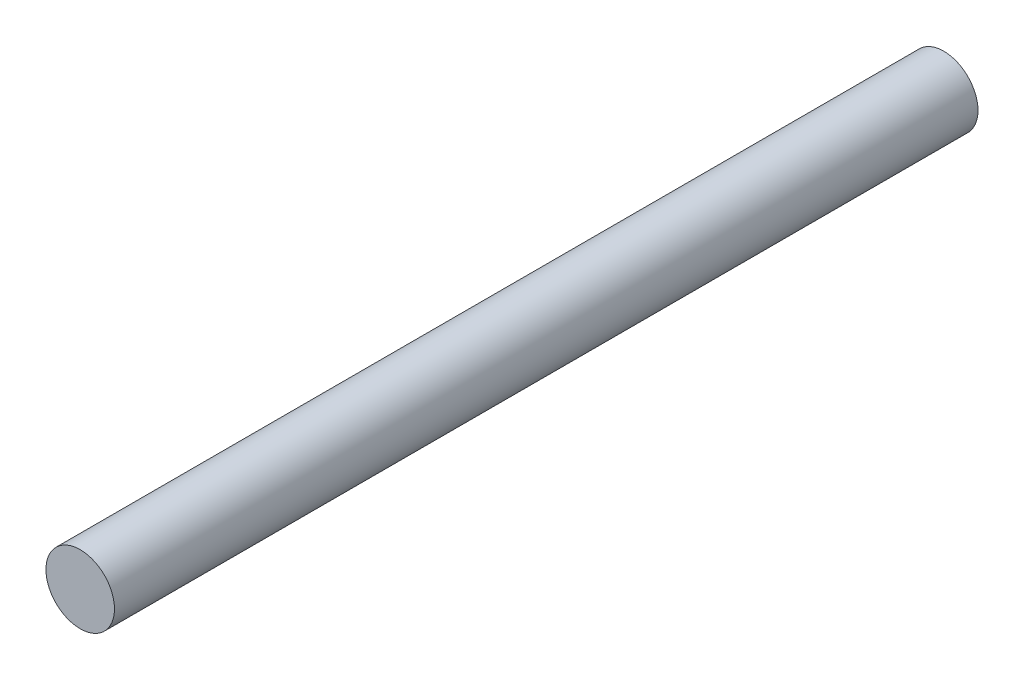
SolidWorks part; units mm, degrees
material "AISI 1020"
ref_plane "Front Plane" through (0, 0, 0) normal (0, 0, 1) x (1, 0, 0)
ref_plane "Top Plane" through (0, 0, 0) normal (0, 1, 0) x (1, 0, 0)
ref_plane "Right Plane" through (0, 0, 0) normal (1, 0, 0) x (0, 0, -1)
sketch "Sketch1" plane through (0, 0, 0) normal (0, 0, 1) x (1, 0, 0)
  circle A0 centre (0, 0) radius 4.7625
  dimension "D1" = 9.525
extrude "Boss-Extrude1" add sketch "Sketch1" along normal blind 120
